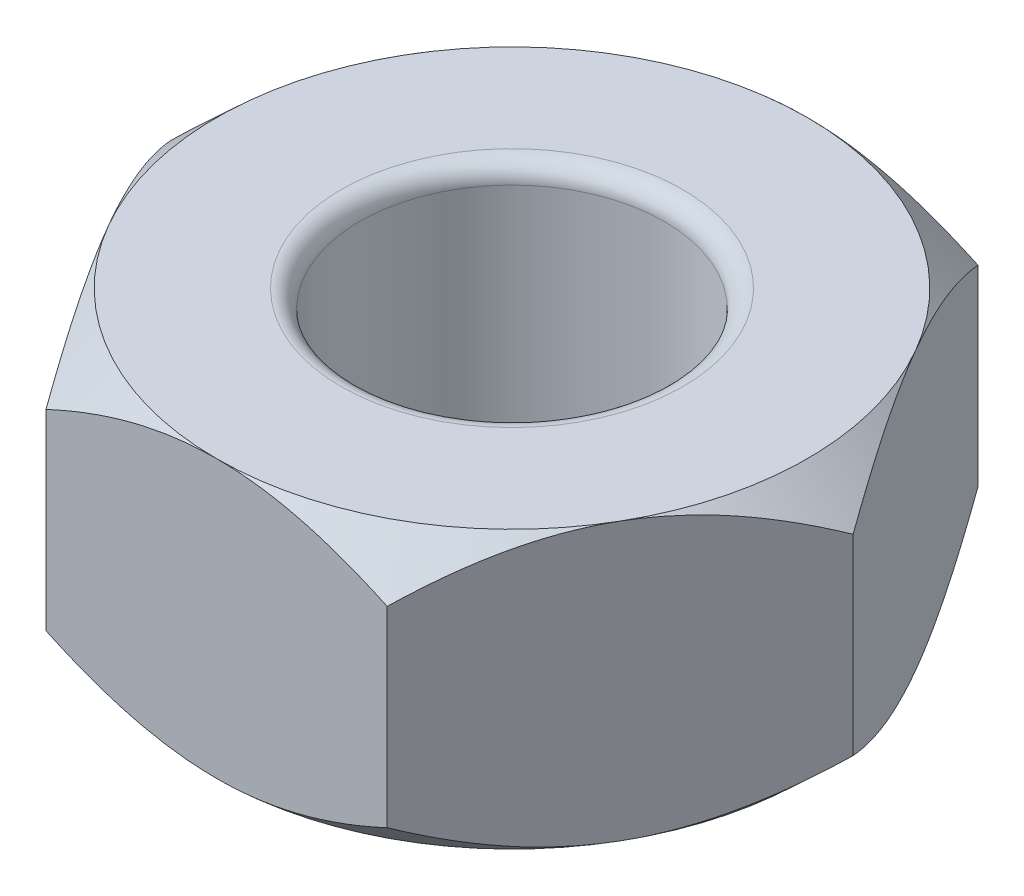
SolidWorks part; units mm, degrees
ref_plane "Alzado" through (0, 0, 0) normal (0, 0, 1) x (1, 0, 0)
ref_plane "Planta" through (0, 0, 0) normal (0, 1, 0) x (1, 0, 0)
ref_plane "Vista lateral" through (0, 0, 0) normal (1, 0, 0) x (0, 0, -1)
sketch "Croquis1" plane through (0, 0, 0) normal (0, 1, 0) x (1, 0, 0)
  line L0 (0, 20.3129) -> (0, -20.6756) construction
  line L2 (18.4752, 0) -> (9.2376, 16)
  line L3 (9.2376, 16) -> (-9.2376, 16)
  line L4 (-9.2376, 16) -> (-18.4752, 0)
  line L5 (-18.4752, 0) -> (-9.2376, -16)
  line L6 (-9.2376, -16) -> (9.2376, -16)
  line L7 (9.2376, -16) -> (18.4752, 0)
  circle A0 centre (0, 0) radius 18.4752
  circle A1 centre (0, 0) radius 16 construction
  dimension "D1" = 32
extrude "Saliente-Extruir1" add sketch "Croquis1" against normal blind 15 contours L6 L7 L2 L3 L4 L5
sketch "Croquis2" plane through (0, 0, 0) normal (0, 1, 0) x (1, 0, 0)
  circle A0 centre (0, 0) radius 16
extrude "Cortar-Extruir1" cut sketch "Croquis2" against normal blind 15 draft 47 flip side to cut
sketch "Croquis3" plane through (0, -15, 0) normal (0, -1, 0) x (1, 0, 0)
  circle A0 centre (0, 0) radius 16
extrude "Cortar-Extruir2" cut sketch "Croquis3" against normal blind 15 draft 47 flip side to cut
sketch "Croquis4" plane through (0, 0, 0) normal (0, 1, 0) x (1, 0, 0)
  circle A0 centre (0, 0) radius 8.25
  dimension "D1" = 16.5
extrude "Cortar-Extruir3" cut sketch "Croquis4" against normal blind 15
fillet "Redondeo1" radius 1 2 edges at (0, -15, 8.25) (0, 0, 8.25)
